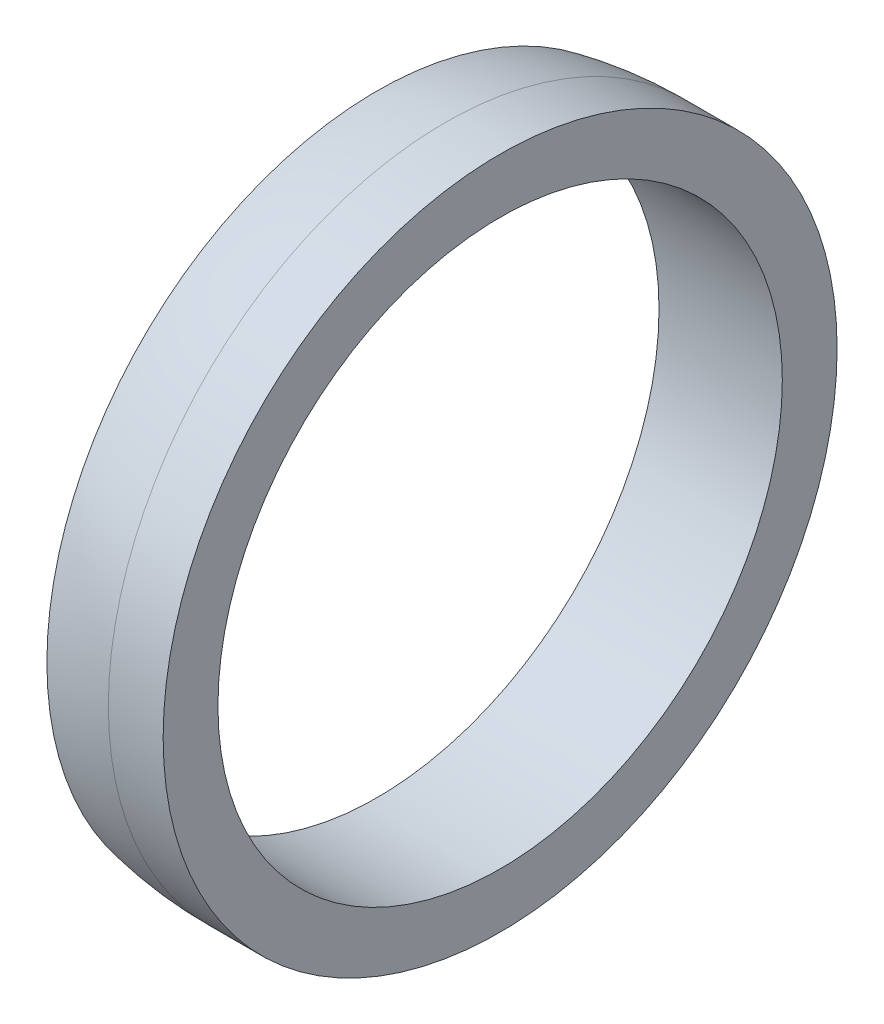
SolidWorks part; units mm, degrees
ref_plane "Ebene vorne" through (0, 0, 0) normal (0, 0, 1) x (1, 0, 0)
ref_plane "Ebene oben" through (0, 0, 0) normal (0, 1, 0) x (1, 0, 0)
ref_plane "Ebene rechts" through (0, 0, 0) normal (1, 0, 0) x (0, 0, -1)
sketch "Skizze2" plane through (0, 0, 0) normal (0, 0, 1) x (1, 0, 0)
  line L2 (0, 246) -> (0, 206)
  line L3 (0, 206) -> (-50, 206)
  line L4 (-50, 240.8651) -> (-50, 206)
  arc A0 (0, 246) -> (0, -246) centre (0, 0) ccw construction
  arc A1 (-50, 240.8651) -> (0, 246) centre (0, 0) cw
  dimension "D1" = 246
  dimension "D2" = 50
  dimension "D3" = 40
ref_axis "Achse1" through (0, 0, 0) along (1, 0, 0)
revolve "Rotation1" add sketch "Skizze2" angle 360 about axis through (0, 0, 0) along (1, 0, 0)
sketch "Skizze4" plane through (0, 0, 0) normal (1, 0, 0) x (0, 0, -1)
  circle A0 centre (0, 0) radius 246
  circle A1 centre (0, 0) radius 206
extrude "Aufsatz-Linear austragen1" add sketch "Skizze4" along normal blind 40
